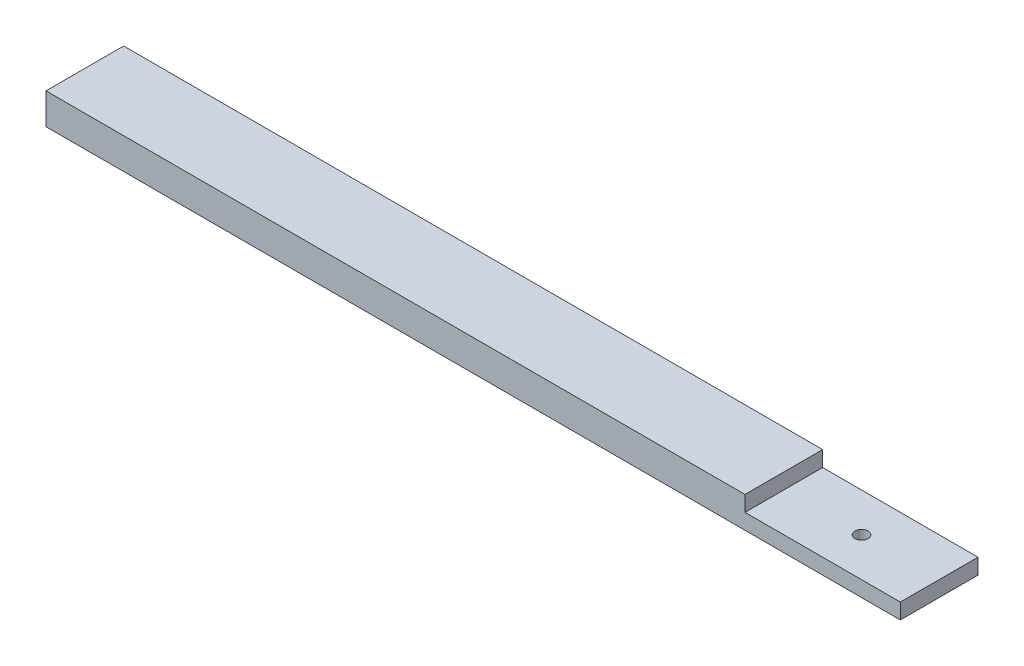
SolidWorks part; units mm, degrees
ref_plane "Front Plane" through (0, 0, 0) normal (0, 0, 1) x (1, 0, 0)
ref_plane "Top Plane" through (0, 0, 0) normal (0, 1, 0) x (1, 0, 0)
ref_plane "Right Plane" through (0, 0, 0) normal (1, 0, 0) x (0, 0, -1)
sketch "Sketch1" plane through (0, 0, 0) normal (0, 1, 0) x (1, 0, 0)
  line L1 (-69.85, 6.35) -> (69.85, 6.35)
  line L2 (-69.85, 6.35) -> (-69.85, -6.35)
  line L3 (-69.85, -6.35) -> (69.85, -6.35)
  line L4 (69.85, 6.35) -> (69.85, -6.35)
  line L5 (-69.85, 6.35) -> (69.85, -6.35) construction
  line L6 (-69.85, -6.35) -> (69.85, 6.35) construction
  point P0 (0, 0)
  dimension "D1" = 12.7
  dimension "D2" = 139.7
extrude "Boss-Extrude1" add sketch "Sketch1" along normal blind 5.08
sketch "Sketch3" plane through (0, 0, 6.35) normal (0, 0, 1) x (1, 0, 0)
  line L1 (69.85, 5.08) -> (44.45, 5.08)
  line L2 (69.85, 5.08) -> (69.85, 2.54)
  line L3 (69.85, 2.54) -> (44.45, 2.54)
  line L4 (44.45, 5.08) -> (44.45, 2.54)
  dimension "D1" = 25.4
extrude "Cut-Extrude1" cut sketch "Sketch3" against normal blind 17.78
sketch "Sketch4" plane through (0, 2.54, 0) normal (0, 1, 0) x (1, 0, 0)
  circle A0 centre (57.15, 0) radius 1.0795
  dimension "D1" = 2.159
extrude "Cut-Extrude2" cut sketch "Sketch4" against normal blind 17.78
